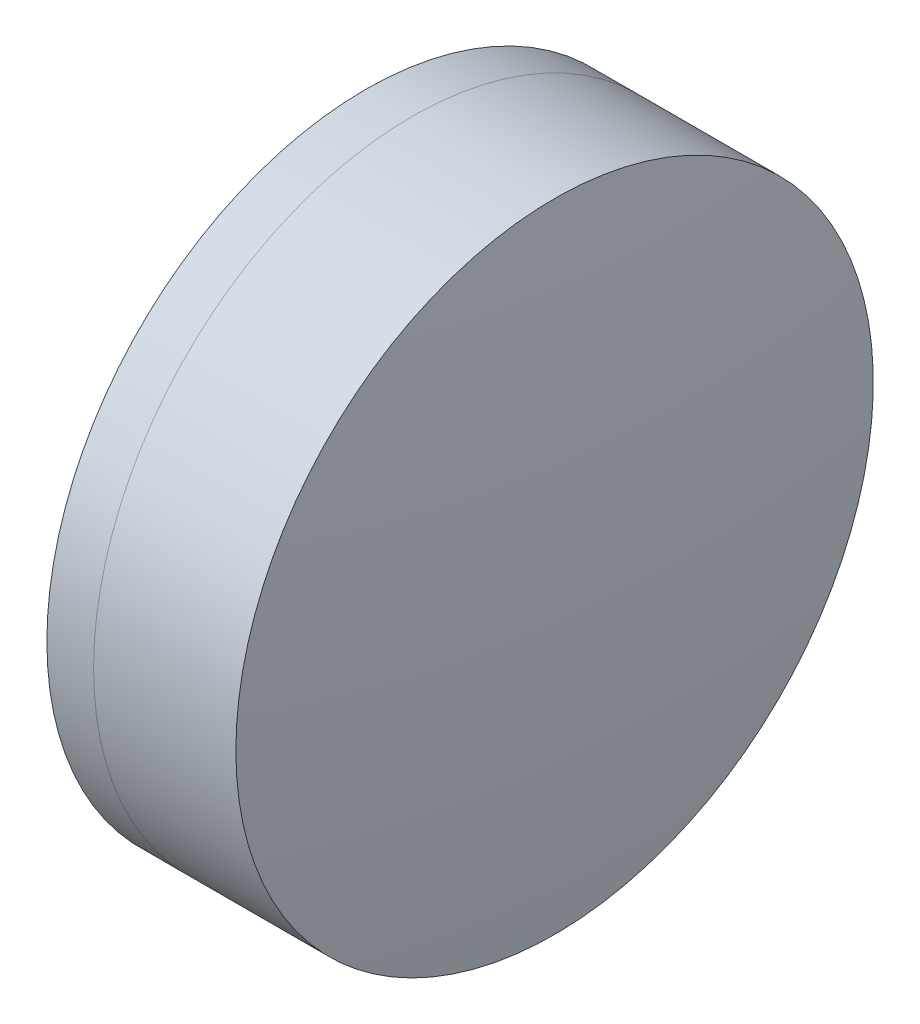
SolidWorks part; units mm, degrees
ref_plane "前视基准面" through (0, 0, 0) normal (0, 0, 1) x (1, 0, 0)
ref_plane "上视基准面" through (0, 0, 0) normal (0, 1, 0) x (1, 0, 0)
ref_plane "右视基准面" through (0, 0, 0) normal (1, 0, 0) x (0, 0, -1)
sketch "草图1" plane through (0, 0, 0) normal (0, 1, 0) x (1, 0, 0)
  line L0 (124.5233, 0) -> (646.9917, 0) construction
  line L1 (276.2363, -12.7) -> (278.0957, -12.7)
  line L2 (276.2363, 12.7) -> (278.0957, 12.7)
  arc A0 (278.0957, -12.7) -> (278.0957, 12.7) centre (264.479, 0) ccw
  arc A1 (276.2363, 12.7) -> (276.2363, -12.7) centre (296.589, 0) ccw
  point P10 (272.599, 0)
  point P11 (283.099, 0)
  dimension "D3" = 23.99
  dimension "D4" = 18.62
  dimension "D1" = 12.7
  dimension "D2" = 12.7
  dimension "D5" = 10.5
revolve "旋转1" add sketch "草图1" angle 360 about L0
sketch "草图2" plane through (0, 0, 0) normal (0, 1, 0) x (1, 0, 0)
  line L0 (-0.5519, 0) -> (622.6607, 0) construction
  line L2 (278.0957, 12.7) -> (283.7663, 12.7)
  line L3 (278.0957, -12.7) -> (283.7663, -12.7)
  arc A0 (283.7663, -12.7) -> (283.7663, 12.7) centre (187.329, 0) ccw
  arc A1 (278.0957, -12.7) -> (278.0957, 12.7) centre (264.479, 0) ccw construction
  arc A2 (278.0957, -12.7) -> (278.0957, 12.7) centre (264.479, 0) ccw
  point P4 (283.099, 0)
  point P8 (284.599, 0)
  dimension "D1" = 97.27
  dimension "D2" = 1.5
revolve "旋转3" add sketch "草图2" angle 360 about L0
